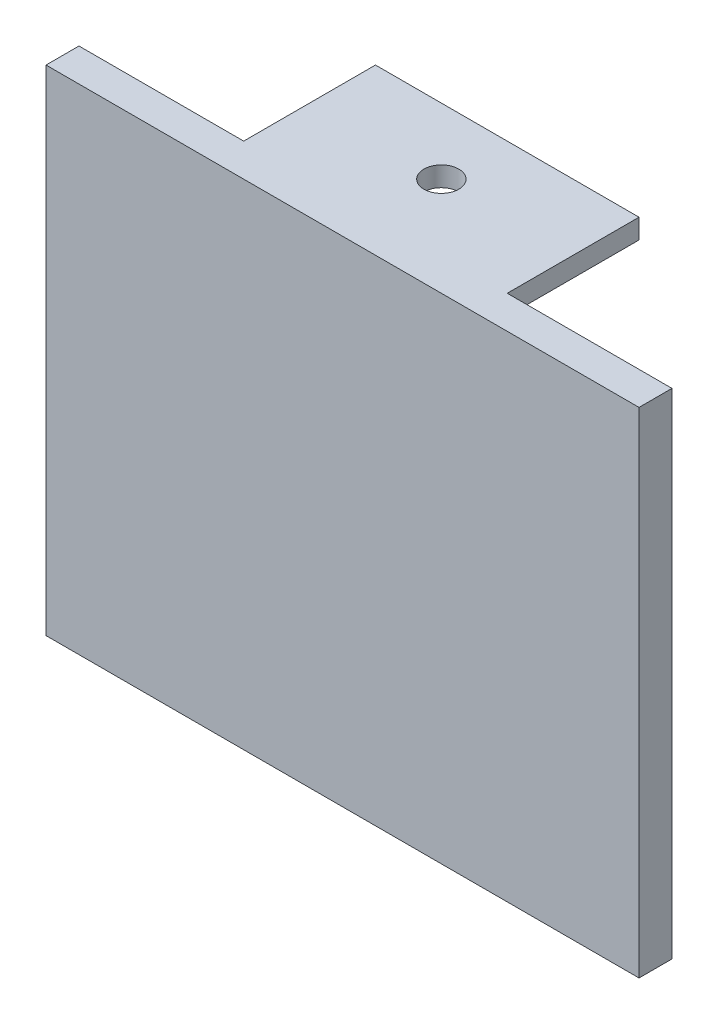
SolidWorks part; units mm, degrees
ref_plane "前视基准面" through (0, 0, 0) normal (0, 0, 1) x (1, 0, 0)
ref_plane "上视基准面" through (0, 0, 0) normal (0, 1, 0) x (1, 0, 0)
ref_plane "右视基准面" through (0, 0, 0) normal (1, 0, 0) x (0, 0, -1)
sketch "草图1" plane through (0, 0, 0) normal (0, 0, 1) x (1, 0, 0)
  line L1 (-46.1686, 20.9195) -> (43.8314, 20.9195)
  line L2 (-46.1686, 20.9195) -> (-46.1686, -54.0805)
  line L3 (-46.1686, -54.0805) -> (43.8314, -54.0805)
  line L4 (43.8314, 20.9195) -> (43.8314, -54.0805)
  dimension "D1" = 90
  dimension "D2" = 75
extrude "凸台-拉伸1" add sketch "草图1" along normal blind 5
sketch "草图3" plane through (0, 0, 0) normal (0, 0, -1) x (-1, 0, 0)
  line L0 (-43.8314, 20.9195) -> (46.1686, 20.9195) construction
  line L1 (-18.8314, 20.9195) -> (21.1686, 20.9195)
  line L2 (-18.8314, 20.9195) -> (-18.8314, 17.9195)
  line L3 (-18.8314, 17.9195) -> (21.1686, 17.9195)
  line L4 (21.1686, 20.9195) -> (21.1686, 17.9195)
  line L5 (-43.8314, -54.0805) -> (-43.8314, 20.9195) construction
  dimension "D1" = 40
  dimension "D2" = 25
  dimension "D3" = 3
extrude "凸台-拉伸2" add sketch "草图3" along normal blind 20
sketch "草图4" plane through (0, 20.9195, 0) normal (0, 1, 0) x (1, 0, 0)
  line L1 (-21.1686, 20) -> (18.8314, 20) construction
  circle A1 centre (-1.1686, 10) radius 2.65
  dimension "D1" = 5.3
  dimension "D2" = 10
extrude "切除-拉伸2" cut sketch "草图4" against normal blind 20
sketch "草图5" plane through (0, 0, 0) normal (0, 0, -1) x (-1, 0, 0)
  line L1 (-41.024, 16.8537) -> (43.976, 16.8537)
  line L2 (-41.024, 16.8537) -> (-41.024, -52.1463)
  line L3 (-41.024, -52.1463) -> (43.976, -52.1463)
  line L4 (43.976, 16.8537) -> (43.976, -52.1463)
  dimension "D1" = 85
  dimension "D2" = 69
extrude "切除-拉伸3" cut sketch "草图5" against normal blind 3
